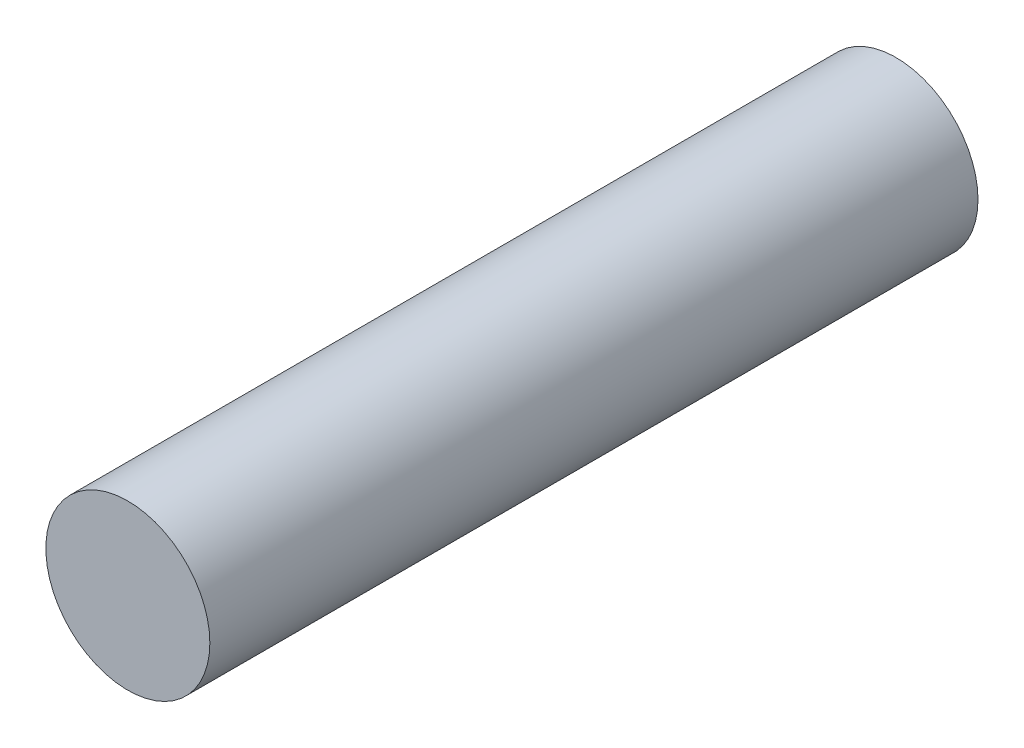
SolidWorks part; units mm, degrees
ref_plane "Piano frontale" through (0, 0, 0) normal (0, 0, 1) x (1, 0, 0)
ref_plane "Piano superiore" through (0, 0, 0) normal (0, 1, 0) x (1, 0, 0)
ref_plane "Piano destro" through (0, 0, 0) normal (1, 0, 0) x (0, 0, -1)
sketch "Sketch1" plane through (0, 0, 0) normal (0, 0, 1) x (1, 0, 0)
  circle A0 centre (0, 0) radius 1.5
  dimension "D1" = 3
extrude "Boss-Extrude1" add sketch "Sketch1" along normal blind 14.05 contours A0
